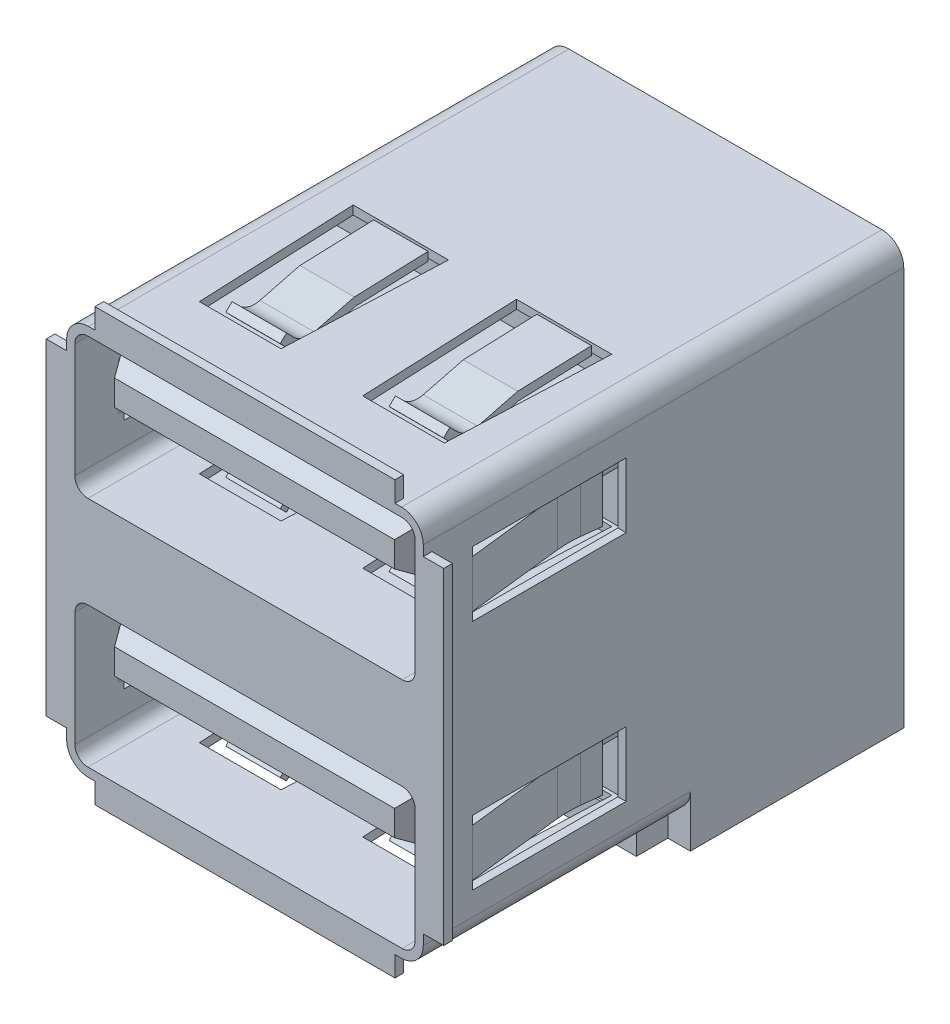
SolidWorks part; units mm, degrees
ref_plane "Front" through (0, 0, 0) normal (0, 0, 1) x (1, 0, 0)
ref_plane "Top" through (0, 0, 0) normal (0, 1, 0) x (1, 0, 0)
ref_plane "Side" through (0, 0, 0) normal (1, 0, 0) x (0, 0, -1)
ref_plane "Position 1 Plane" through (-3.5, 0, 0) normal (1, 0, 0) x (0, 0, -1)
sketch "Sketch1" plane through (0, 0, 0) normal (0, 1, 0) x (1, 0, 0)
  line L0 (6.55, -8.825) -> (-6.55, 8.825) construction
  line L1 (-6.55, 8.825) -> (6.55, 8.825)
  line L2 (-6.55, 8.825) -> (-6.55, -8.825)
  line L3 (-6.55, -8.825) -> (6.55, -8.825)
  line L4 (6.55, 8.825) -> (6.55, -8.825)
  dimension "D1" = 13.1
  dimension "D2" = 17.65
extrude "Base" add sketch "Sketch1" along normal blind 14.35
ref_plane "Ground Tail Plane" through (0, 0, -1.885) normal (0, 0, 1) x (1, 0, 0)
ref_plane "Top/Bottom Flange Plane" through (-3, 0, 0) normal (1, 0, 0) x (0, 0, -1)
ref_plane "Mid Plane" through (0, 2.85, 0) normal (0, 1, 0) x (-1, 0, 0)
ref_plane "Back Plane" through (0, 0, -8.825) normal (0, 0, 1) x (1, 0, 0)
ref_plane "Cut Plane" through (0, 0, -0.075) normal (0, 0, 1) x (1, 0, 0)
sketch "Sketch3" plane through (0, 0, 8.825) normal (0, 0, 1) x (1, 0, 0)
  line L0 (-6.55, 14.35) -> (6.55, 14.35) construction
  line L1 (-5.51, 14.35) -> (5.51, 14.35)
  line L2 (-5.51, 14.35) -> (-5.51, 15.1)
  line L3 (-5.51, 15.1) -> (5.51, 15.1)
  line L4 (5.51, 14.35) -> (5.51, 15.1)
  line L5 (6.55, 14.35) -> (6.55, 0) construction
  line L6 (6.55, 13.175) -> (7.3, 13.175)
  line L7 (6.55, 13.175) -> (6.55, 1.175)
  line L8 (6.55, 1.175) -> (7.3, 1.175)
  line L9 (7.3, 13.175) -> (7.3, 1.175)
  line L10 (0, 15.1) -> (0, 14.35) construction
  line L11 (6.55, 7.175) -> (7.3, 7.175) construction
  line L12 (-6.55, 14.35) -> (6.55, 0) construction
  line L13 (0, 7.175) -> (3.5942, 7.175) construction
  line L14 (5.51, 0) -> (5.51, -0.75)
  line L15 (-5.51, -0.75) -> (5.51, -0.75)
  line L16 (-5.51, 0) -> (-5.51, -0.75)
  line L17 (-5.51, 0) -> (5.51, 0)
  line L18 (0, 7.175) -> (0, 4.7958) construction
  line L19 (-7.3, 13.175) -> (-7.3, 1.175)
  line L20 (-6.55, 1.175) -> (-7.3, 1.175)
  line L21 (-6.55, 13.175) -> (-6.55, 1.175)
  line L22 (-6.55, 13.175) -> (-7.3, 13.175)
  dimension "D1" = 14.6
  dimension "D2" = 11.02
  dimension "D3" = 15.85
  dimension "D4" = 12
extrude "Front Tabs" add sketch "Sketch3" against normal blind 0.32
fillet "Corner Fillets" radius 0.8 4 edges at (-6.55, 14.35, 0) (-6.55, 0, 0) (6.55, 0, 0) (6.55, 14.35, 0)
sketch "Sketch18" plane through (0, 0, -8.825) normal (0, 0, -1) x (-1, 0, 0)
  line L0 (-6.55, 0.8) -> (-6.55, -1.1)
  line L1 (-6.55, -1.1) -> (6.55, -1.1)
  line L2 (6.55, -1.1) -> (6.55, 0.8)
  line L3 (-5.75, 0) -> (5.75, 0) construction
  line L4 (-5.75, 0) -> (5.75, 0)
  line L5 (0, 0) -> (0, -1.6279) construction
  arc A2 (-6.55, 0.8) -> (-5.75, 0) centre (-5.75, 0.8) ccw
  arc A3 (5.75, 0) -> (6.55, 0.8) centre (5.75, 0.8) ccw
  point P13 (0, -1.1)
  dimension "D2" = 0.8
  dimension "D1" = 1.1
extrude "-D Back Step" add sketch "Sketch18" against normal blind 7.84
sketch "Sketch19" plane through (0, 0, 0) normal (0, -1, 0) x (1, 0, 0)
  line L0 (6.55, -0.985) -> (-6.55, -0.985) construction
  line L1 (5.725, -0.985) -> (-5.725, -0.985)
  line L2 (5.725, -0.985) -> (5.725, 0.175)
  line L3 (5.725, 0.175) -> (-5.725, 0.175)
  line L4 (-5.725, -0.985) -> (-5.725, 0.175)
  line L5 (0, 0.175) -> (0, -0.985) construction
  line L6 (6.55, -8.825) -> (-6.55, -8.825) construction
  dimension "D1" = 9
  dimension "D2" = 11.45
extrude "-D Bottom Step" add sketch "Sketch19" along normal up to surface (1.1 mm away) up to face at (0, -1.1, -4.905)
sketch "Sketch23" plane through (0, 0, 0) normal (0, -1, 0) x (1, 0, 0)
  line L0 (-3.5098, -4.4478) -> (-3.5098, -4.7578) construction
  line L1 (-3.1796, -4.4478) -> (-3.84, -4.4478)
  line L2 (-3.1796, -4.4478) -> (-3.1796, -4.7578)
  line L3 (-3.1796, -4.7578) -> (-3.84, -4.7578)
  line L4 (-3.84, -4.4478) -> (-3.84, -4.7578)
  line L5 (-3.1796, -4.6028) -> (-3.84, -4.6028) construction
  line L6 (3.16, -4.4478) -> (3.16, -4.7578)
  line L7 (3.8204, -4.4478) -> (3.16, -4.4478)
  line L8 (3.8204, -4.4478) -> (3.8204, -4.7578)
  line L9 (3.8204, -4.7578) -> (3.16, -4.7578)
  line L10 (-1.34, -4.4478) -> (-1.34, -4.7578)
  line L11 (-0.6796, -4.4478) -> (-1.34, -4.4478)
  line L12 (-0.6796, -4.4478) -> (-0.6796, -4.7578)
  line L13 (-0.6796, -4.7578) -> (-1.34, -4.7578)
  line L14 (0.66, -4.4478) -> (0.66, -4.7578)
  line L15 (1.3204, -4.4478) -> (0.66, -4.4478)
  line L16 (1.3204, -4.4478) -> (1.3204, -4.7578)
  line L17 (1.3204, -4.7578) -> (0.66, -4.7578)
  line L18 (0, 0) -> (0, -8.093) construction
  line L19 (7.92, -1.885) -> (-7.92, -1.885) construction
  dimension "D1" = 2.5
  dimension "D2" = 2
  dimension "D3" = 2.5
  dimension "D4" = 0.31
  dimension "D5" = 1.34
  dimension "D6" = 0.6604
  dimension "D7" = 2.7178
extrude "-TH Contact Tail" [suppressed] add sketch "Sketch23" along normal blind 4.1
pattern_linear "-TH Contact Pattern" [suppressed] count 2 spacing 2.62
sketch "Sketch8" plane through (0, 0, 8.825) normal (0, 0, 1) x (1, 0, 0)
  line L0 (-6.25, 5) -> (-6.25, 0.8)
  line L1 (-5.77, 0.32) -> (5.77, 0.32)
  line L2 (-5.77, 5.48) -> (5.77, 5.48)
  line L3 (6.25, 0.8) -> (6.25, 5)
  line L4 (0, 0) -> (0, 6.7662) construction
  arc A16 (6.25, 5) -> (5.77, 5.48) centre (5.77, 5) ccw
  arc A17 (5.77, 0.32) -> (6.25, 0.8) centre (5.77, 0.8) ccw
  arc A18 (-6.25, 0.8) -> (-5.77, 0.32) centre (-5.77, 0.8) ccw
  arc A19 (-5.77, 5.48) -> (-6.25, 5) centre (-5.77, 5) ccw
  point P4 (0, 5.48)
  dimension "D2" = 0.48
  dimension "D1" = 12.5
  dimension "D3" = 0.32
  dimension "D4" = 5.16
extrude "Contact Area Cutout" cut sketch "Sketch8" against normal blind 8.85
sketch "Sketch12" plane through (0, 0, 0) normal (0, 1, 0) x (-1, 0, 0)
  line L0 (0, 0) -> (0, 5.7946) construction
  line L1 (4.5, 6) -> (4.75, 0.1)
  line L2 (3, 4.5748) -> (3, 0.3752) construction
  line L3 (1.5, 6) -> (1.25, 0.1)
  line L4 (4.5, 6) -> (1.5, 6)
  line L5 (4.75, 0.1) -> (1.25, 0.1)
  line L7 (-4.75, 0.1) -> (-1.25, 0.1)
  line L8 (-4.5, 6) -> (-1.5, 6)
  line L9 (-1.5, 6) -> (-1.25, 0.1)
  line L10 (-4.5, 6) -> (-4.75, 0.1)
  dimension "D1" = 3.5
  dimension "D2" = 3
  dimension "D3" = 5.9
  dimension "D4" = 6
  dimension "D5" = 3
extrude "Top/Bottom Flange Cutout" cut sketch "Sketch12" along normal blind 5.8
sketch "Sketch13" plane through (-3, 0, 0) normal (1, 0, 0) x (0, 0, -1)
  line L0 (-2.7601, 0.4175) -> (-4.1983, 0.7842)
  line L1 (7.05, 2.85) -> (-8.6639, 2.85) construction
  line L2 (-2.8059, 5.6011) -> (-4.2773, 5.2259)
  line L3 (-5.0476, 5.4424) -> (-5.3, 5.7011)
  line L4 (-5.2766, 5.2189) -> (-5.529, 5.4776)
  line L5 (-2.7601, 5.2825) -> (-4.1983, 4.9158)
  line L6 (-2.8059, 5.6011) -> (-0.1, 5.699)
  line L7 (-5.529, 5.4776) -> (-5.3, 5.7011)
  line L8 (-0.1, 5.699) -> (-0.1, 5.3788)
  line L9 (0.985, 0) -> (-8.825, 0) construction
  line L10 (-5.3, 5.7011) -> (-5.3, -0.0011) construction
  line L12 (-2.7601, 0.4175) -> (-0.1, 0.3212)
  line L13 (-0.1, 0.001) -> (-0.1, 0.3212)
  line L14 (-5.529, 0.2224) -> (-5.3, -0.0011)
  line L15 (-2.8059, 0.0989) -> (-0.1, 0.001)
  line L16 (-5.2766, 0.4811) -> (-5.529, 0.2224)
  line L17 (-2.7601, 5.2825) -> (-0.1, 5.3788)
  line L18 (-5.0476, 0.2576) -> (-5.3, -0.0011)
  line L19 (-2.8059, 0.0989) -> (-4.2773, 0.4741)
  line L20 (0.6313, 2.85) -> (-0.6313, 2.85) construction
  arc A0 (-4.2773, 5.2259) -> (-5.0476, 5.4424) centre (-4.475, 6.0011) cw
  arc A1 (-4.1983, 4.9158) -> (-5.2766, 5.2189) centre (-4.475, 6.0011) cw
  arc A2 (-4.1983, 0.7842) -> (-5.2766, 0.4811) centre (-4.475, -0.3011) ccw
  arc A3 (-4.2773, 0.4741) -> (-5.0476, 0.2576) centre (-4.475, -0.3011) ccw
  point P15 (-5.3, 2.85)
  dimension "D3" = 0.8
  dimension "D6" = 5.2
  dimension "D8" = 0.4
  dimension "D2" = 4.375
  dimension "D4" = 2.7059
  dimension "D5" = 0.32
  dimension "D7" = 0.3614
  dimension "D9" = 0.32
  dimension "D10" = 5.7021
  dimension "D11" = 0.1
  dimension "D13" = 0.001
extrude "Top/Bottom Flange" add sketch "Sketch13" along normal mid plane 2
pattern_linear "Top/Bottom Flange Pattern" count 2 spacing 6 along (1, 0, 0) of "Top/Bottom Flange"
sketch "Sketch14" plane through (6.55, 0, 0) normal (1, 0, 0) x (0, 0, -1)
  line L0 (0.6313, 2.85) -> (-0.6313, 2.85) construction
  line L1 (-7.025, 4.04) -> (-1.375, 4.04)
  line L2 (-7.025, 4.04) -> (-7.025, 1.66)
  line L3 (-7.025, 1.66) -> (-1.375, 1.66)
  line L4 (-1.375, 4.04) -> (-1.375, 1.66)
  line L7 (7.05, 2.85) -> (-7.9068, 2.85) construction
  line L8 (-8.825, 1.175) -> (-8.825, 0.8) construction
  point P4 (-7.025, 2.85)
  dimension "D1" = 2.38
  dimension "D2" = 5.65
  dimension "D3" = 1.8
extrude "Side Flange Cutout" cut sketch "Sketch14" against normal through all
sketch "Sketch15" plane through (0, 2.85, 0) normal (0, 1, 0) x (-1, 0, 0)
  line L0 (6.55, 7.025) -> (6.149, 3.4987)
  line L1 (6.1488, 2.6528) -> (6.2313, 1.925)
  line L2 (6.55, 7.025) -> (6.25, 7.025) construction
  line L3 (6.55, 8.825) -> (6.55, -8.825) construction
  line L4 (5.8309, 2.6168) -> (5.9133, 1.889)
  line L5 (6.25, 7.219) -> (5.8311, 3.5348)
  line L6 (6.25, 7.219) -> (6.55, 7.025)
  line L7 (5.9133, 1.889) -> (6.2313, 1.925)
  line L8 (0, 0) -> (0, 6.0458) construction
  line L9 (-5.9133, 1.889) -> (-6.2313, 1.925)
  line L10 (-6.25, 7.219) -> (-6.55, 7.025)
  line L11 (-6.25, 7.219) -> (-5.8311, 3.5348)
  line L12 (-5.8309, 2.6168) -> (-5.9133, 1.889)
  line L13 (-6.1488, 2.6528) -> (-6.2313, 1.925)
  line L14 (-6.55, 7.025) -> (-6.149, 3.4987)
  line L15 (6.25, -0.025) -> (6.25, 8.825) construction
  arc A0 (6.149, 3.4987) -> (6.1488, 2.6528) centre (9.875, 3.075) ccw
  arc A1 (5.8311, 3.5348) -> (5.8309, 2.6168) centre (9.875, 3.075) ccw
  arc A2 (-5.8311, 3.5348) -> (-5.8309, 2.6168) centre (-9.875, 3.075) cw
  arc A3 (-6.149, 3.4987) -> (-6.1488, 2.6528) centre (-9.875, 3.075) cw
  dimension "D2" = 3.75
  dimension "D3" = 3.95
  dimension "D4" = 3.325
  dimension "D6" = 3.6437
  dimension "D1" = 5.1
  dimension "D5" = 0.32
extrude "Side Flange" add sketch "Sketch15" along normal mid plane 1.75
sketch "Sketch16" plane through (0, 0, -0.025) normal (0, 0, 1) x (1, 0, 0)
  line L0 (0, 4.72) -> (0, 2.92) construction
  line L1 (-5.575, 4.72) -> (5.575, 4.72)
  line L2 (-5.575, 4.72) -> (-5.575, 2.92)
  line L3 (-5.575, 2.92) -> (5.575, 2.92)
  line L4 (5.575, 4.72) -> (5.575, 2.92)
  line L6 (5.77, 5.48) -> (-5.77, 5.48) construction
  dimension "D1" = 2.56
  dimension "D3" = 1.8
  dimension "D4" = 11.15
extrude "Contact Guide" add sketch "Sketch16" along normal blind 8.5
chamfer "Contact Guide Lead-in" distance 0.75 angle 30 4 edges at (0, 2.92, 8.475) (-5.575, 3.82, 8.475) (0, 4.72, 8.475) (5.575, 3.82, 8.475)
sketch "Sketch17" plane through (-3.5, 0, 0) normal (1, 0, 0) x (0, 0, -1)
  line L0 (0.025, 3.91) -> (0.025, 3.65)
  line L1 (0.025, 4.72) -> (0.025, 2.92) construction
  line L2 (0.025, 3.65) -> (-1.225, 3.65)
  line L3 (-1.225, 3.65) -> (-4.7879, 2.5075)
  line L4 (-6.6912, 2.7571) -> (-7.225, 3.1)
  line L9 (0.025, 0.8) -> (0.025, 5) construction
  line L10 (-6.5507, 2.9758) -> (-7.0845, 3.3187)
  line L11 (-1.2657, 3.91) -> (-4.8673, 2.755)
  line L12 (0.025, 3.91) -> (-1.2657, 3.91)
  line L13 (-7.725, 2.92) -> (0.025, 2.92) construction
  line L15 (-7.225, 3.1) -> (-7.0845, 3.3187)
  arc A0 (-4.7879, 2.5075) -> (-6.6912, 2.7571) centre (-5.475, 4.65) cw
  arc A1 (-4.8673, 2.755) -> (-6.5507, 2.9758) centre (-5.475, 4.65) cw
  dimension "D5" = 2.25
  dimension "D6" = 1
  dimension "D7" = 4.25
  dimension "D2" = 0.73
  dimension "D4" = 1.25
  dimension "D8" = 0.55
  dimension "D9" = 6
  dimension "D10" = 0.26
extrude "Contact" add sketch "Sketch17" along normal mid plane 0.66
pattern_linear "Contact Pattern" count 2 spacing 2.5 along (1, 0, 0) of "Contact"
mirror "Contact Pattern Mirror" about plane through (0, 0, 0) normal (1, 0, 0) of "Contact", "Contact Pattern"
pattern_linear "Top USB Pattern" count 2 spacing 8.55 along (0, 1, 0) of "Contact Area Cutout", "Top/Bottom Flange Cutout", "Top/Bottom Flange", "Top/Bottom Flange Pattern", "Side Flange Cutout", "Side Flange", "Contact Guide", "Contact Guide Lead-in", "Contact", "Contact Pattern", "Contact Pattern Mirror"
ref_plane "Plane1" through (0, 12.85, 0) normal (0, 1, 0) x (1, 0, 0)
ref_plane "Plane2" through (0, 10.965, 0) normal (0, 1, 0) x (1, 0, 0)
